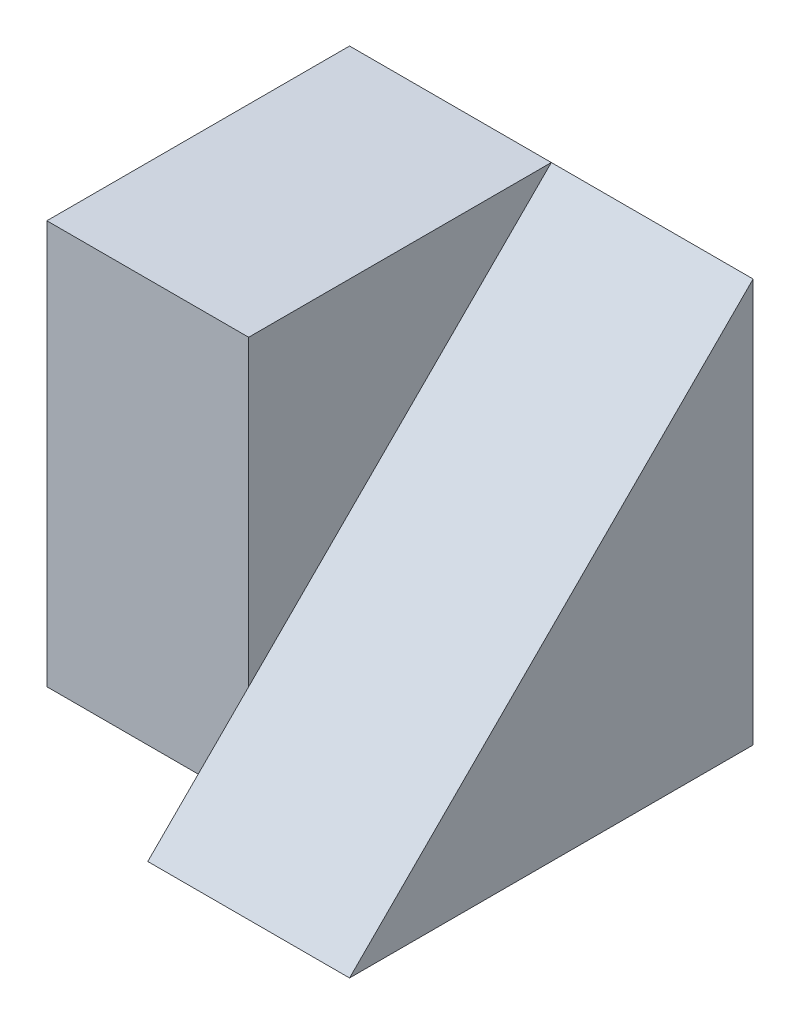
SolidWorks part; units mm, degrees
ref_plane "Front Plane" through (0, 0, 0) normal (0, 0, 1) x (1, 0, 0)
ref_plane "Top Plane" through (0, 0, 0) normal (0, 1, 0) x (1, 0, 0)
ref_plane "Right Plane" through (0, 0, 0) normal (1, 0, 0) x (0, 0, -1)
sketch "Sketch1" plane through (0, 0, 0) normal (1, 0, 0) x (0, 0, -1)
  line L1 (0, 0) -> (4, 0)
  line L2 (0, 0) -> (0, 4)
  line L3 (0, 4) -> (4, 4)
  line L4 (4, 0) -> (4, 4)
  dimension "D1" = 4
  dimension "D2" = 4
extrude "Boss-Extrude1" add sketch "Sketch1" along normal blind 2
sketch "Sketch2" plane through (0, 0, 0) normal (-1, 0, 0) x (0, 0, 1)
  line L0 (-1, 0) -> (-1, 4)
  line L1 (0, 0) -> (-4, 0) construction
  line L2 (-4, 0) -> (-4, 4) construction
  line L3 (-4, 4) -> (-4, 0)
  line L4 (-4, 0) -> (-1, 0)
  line L5 (-4, 4) -> (0, 4) construction
  line L6 (-1, 4) -> (-4, 4)
  dimension "D1" = 3
  dimension "D2" = 4
extrude "Boss-Extrude2" add sketch "Sketch2" along normal blind 2
sketch "Sketch3" plane through (2, 0, 0) normal (1, 0, 0) x (0, 0, -1)
  line L0 (0, 0) -> (4, 4)
  line L1 (4, 4) -> (0, 4)
  line L2 (0, 4) -> (0, 0)
extrude "Cut-Extrude1" cut sketch "Sketch3" against normal blind 2
